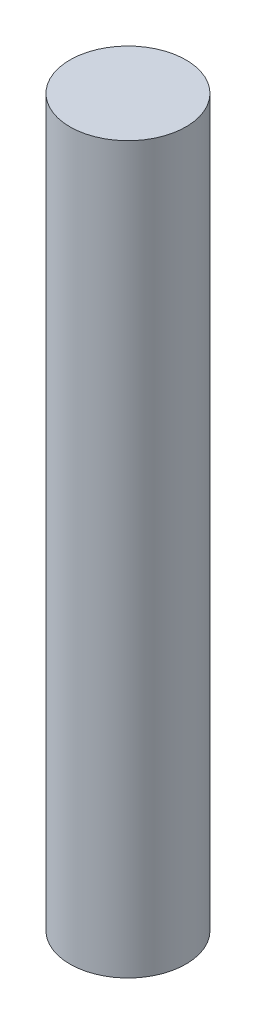
SolidWorks part; units mm, degrees
ref_plane "Front Plane" through (0, 0, 0) normal (0, 0, 1) x (1, 0, 0)
ref_plane "Top Plane" through (0, 0, 0) normal (0, 1, 0) x (1, 0, 0)
ref_plane "Right Plane" through (0, 0, 0) normal (1, 0, 0) x (0, 0, -1)
sketch "Sketch1" plane through (0, 0, 0) normal (0, 1, 0) x (1, 0, 0)
  circle A0 centre (0, 0) radius 6.35
  dimension "D1" = 12.7
extrude "Boss-Extrude1" add sketch "Sketch1" along normal blind 79.375
sketch "Sketch2" plane through (0, 0, 0) normal (0, -1, 0) x (-1, 0, 0)
  circle A0 centre (0, 0) radius 3.8894
  dimension "D1" = 7.7788
extrude "Cut-Extrude1" cut sketch "Sketch2" against normal blind 31.75
